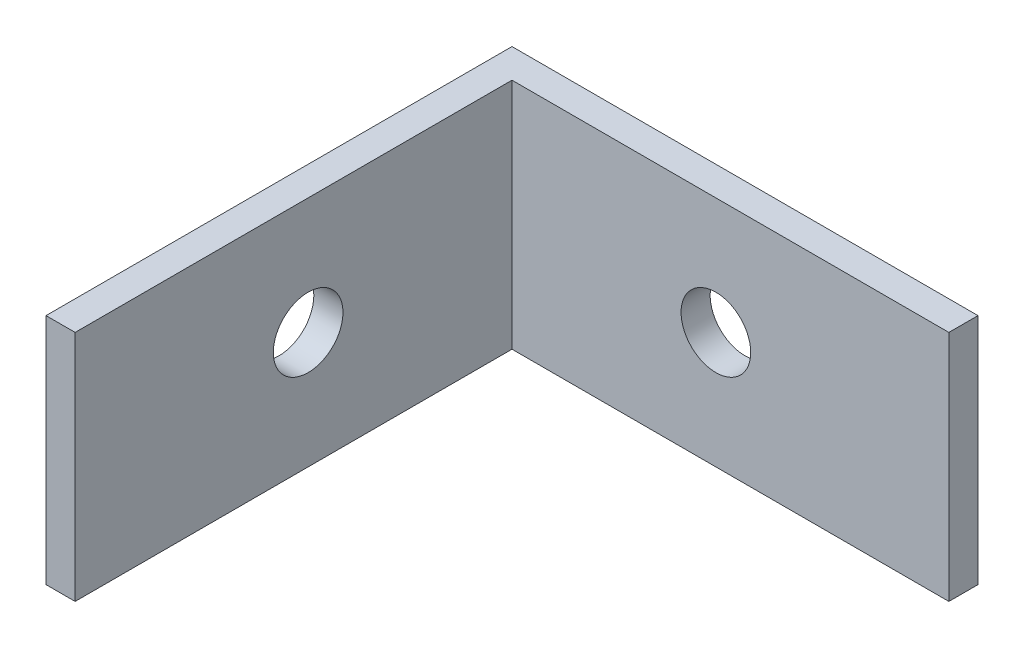
SolidWorks part; units mm, degrees
material "6061-T6 (SS)"
ref_plane "Front Plane" through (0, 0, 0) normal (0, 0, 1) x (1, 0, 0)
ref_plane "Top Plane" through (0, 0, 0) normal (0, 1, 0) x (1, 0, 0)
ref_plane "Right Plane" through (0, 0, 0) normal (1, 0, 0) x (0, 0, -1)
sketch "Sketch1" plane through (0, 0, 0) normal (0, 1, 0) x (1, 0, 0)
  line L0 (0, -5.2552) -> (0, 20.1448)
  line L1 (0, 20.1448) -> (25.4, 20.1448)
  line L2 (25.4, 20.1448) -> (25.4, 18.5573)
  line L3 (25.4, 18.5573) -> (1.5875, 18.5573)
  line L4 (1.5875, 18.5573) -> (1.5875, -5.2552)
  line L5 (1.5875, -5.2552) -> (0, -5.2552)
  dimension "D1" = 25.4
  dimension "D2" = 1.5875
extrude "Boss-Extrude1" add sketch "Sketch1" along normal blind 12.7
hole_wizard "#6 Clearance Hole2" positions "Sketch4" profile "Sketch2" hole size "#6" standard "ANSI Inch" end condition through all
sketch "Sketch4" plane through (1.5875, 0, 0) normal (1, 0, 0) x (0, 0, -1)
  line L0 (-5.2552, 12.7) -> (-5.2552, 0) construction
  line L1 (-5.2552, 12.7) -> (18.5573, 12.7) construction
  point P0 (7.4448, 6.35)
  point P3 (-5.2552, 6.35)
  dimension "D1" = 12.7
  dimension "D2" = 6.35
sketch "Sketch2" plane through (1.5875, 6.35, -7.4448) normal (0, 1, 0) x (0, 0, -1)
  line L0 (0, 0) -> (0, 1.5875)
  line L1 (0, 1.5875) -> (1.8986, 1.5875)
  line L2 (1.8986, 1.5875) -> (1.8986, 0)
  line L5 (1.8986, 0) -> (0, 0)
  line L11 (0, -6.35) -> (0, 107.95) construction
  dimension "Thru Hole Dia." = 3.7973
  dimension "Thru Hole Depth" = 1.5875
hole_wizard "#6 Clearance Hole1" positions "Sketch6" profile "Sketch5" hole size "#6" standard "ANSI Inch" end condition through all
sketch "Sketch6" plane through (0, 0, -18.5573) normal (0, 0, 1) x (1, 0, 0)
  line L0 (25.4, 12.7) -> (25.4, 0) construction
  line L1 (1.5875, 12.7) -> (25.4, 12.7) construction
  point P0 (12.7, 6.35)
  dimension "D1" = 12.7
  dimension "D2" = 6.35
sketch "Sketch5" plane through (12.7, 6.35, -18.5573) normal (1, 0, 0) x (0, -1, 0)
  line L0 (0, 0) -> (0, 1.5875)
  line L1 (0, 1.5875) -> (1.8986, 1.5875)
  line L2 (1.8986, 1.5875) -> (1.8986, 0)
  line L5 (1.8986, 0) -> (0, 0)
  line L11 (0, -6.35) -> (0, 107.95) construction
  dimension "Thru Hole Dia." = 3.7973
  dimension "Thru Hole Depth" = 1.5875
